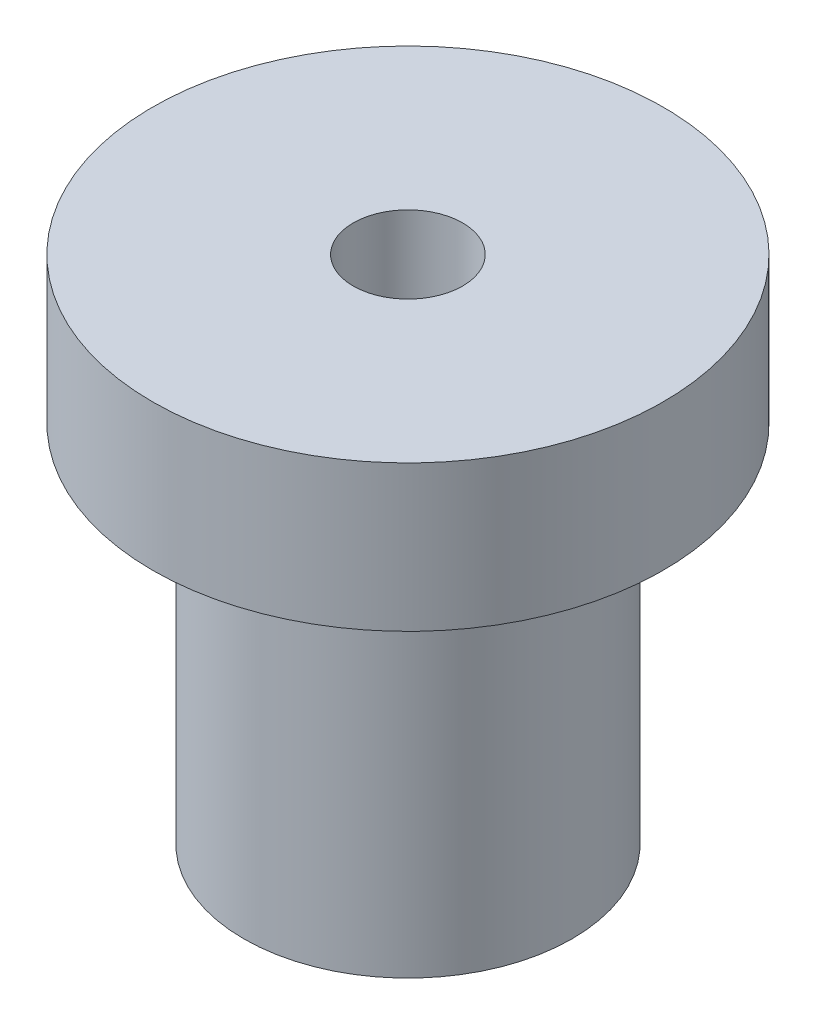
SolidWorks part; units mm, degrees
ref_plane "Front Plane" through (0, 0, 0) normal (0, 0, 1) x (1, 0, 0)
ref_plane "Top Plane" through (0, 0, 0) normal (0, 1, 0) x (1, 0, 0)
ref_plane "Right Plane" through (0, 0, 0) normal (1, 0, 0) x (0, 0, -1)
sketch "Sketch1" plane through (0, 0, 0) normal (0, 1, 0) x (1, 0, 0)
  circle A0 centre (0, 0) radius 9
  dimension "D1" = 18
extrude "Boss-Extrude1" add sketch "Sketch1" along normal blind 20
sketch "Sketch2" plane through (0, 0, 0) normal (0, -1, 0) x (1, 0, 0)
  circle A0 centre (0, 0) radius 3
  dimension "D1" = 6
extrude "Cut-Extrude1" cut sketch "Sketch2" against normal blind 52
sketch "Sketch3" plane through (0, 20, 0) normal (0, 1, 0) x (1, 0, 0)
  circle A0 centre (0, 0) radius 14
  dimension "D1" = 28
extrude "Boss-Extrude2" add sketch "Sketch3" along normal blind 8
sketch "Sketch4" plane through (0, 28, 0) normal (0, 1, 0) x (1, 0, 0)
  circle A0 centre (0, 0) radius 3
  dimension "D1" = 6
extrude "Cut-Extrude2" cut sketch "Sketch4" against normal blind 12
